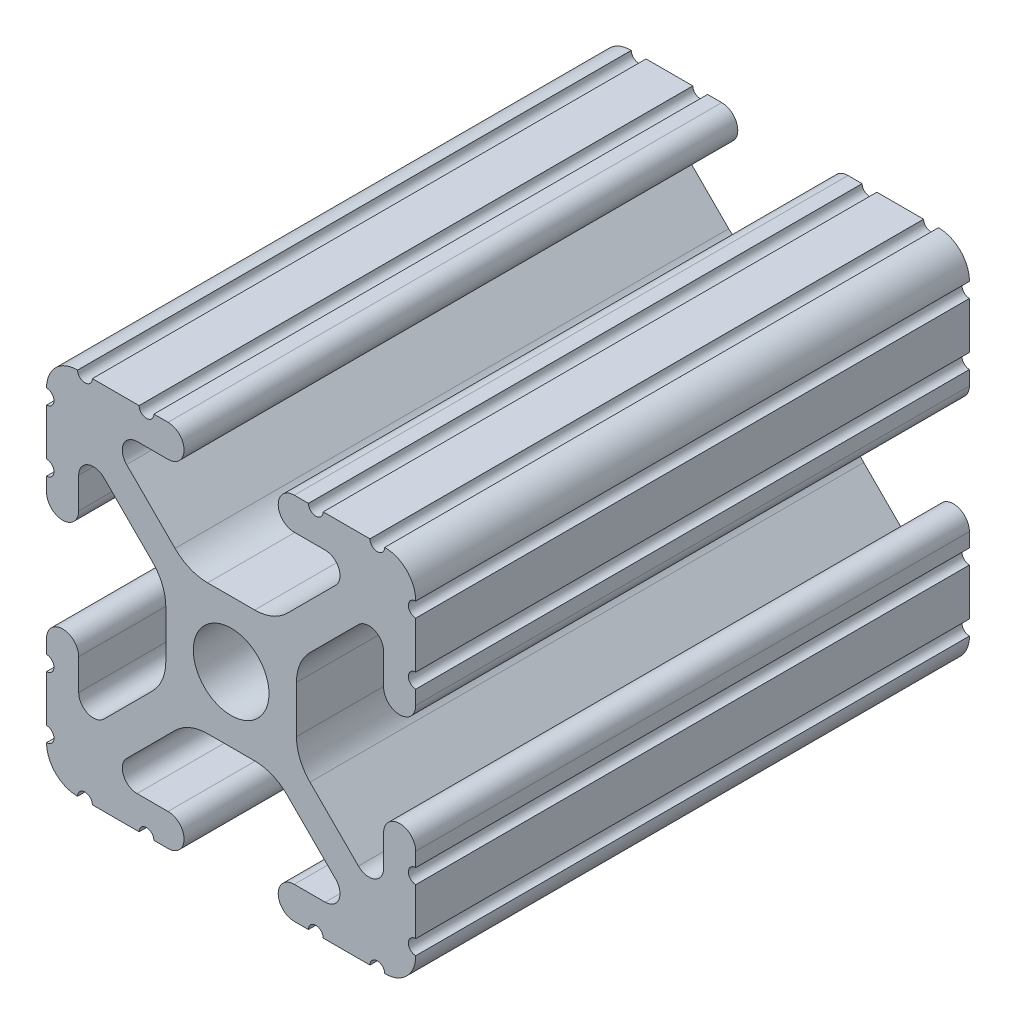
SolidWorks part; units mm, degrees
material "6061-T6 (SS)"
ref_plane "Front Plane" through (0, 0, 0) normal (0, 0, 1) x (1, 0, 0)
ref_plane "Top Plane" through (0, 0, 0) normal (0, 1, 0) x (1, 0, 0)
ref_plane "Right Plane" through (0, 0, 0) normal (1, 0, 0) x (0, 0, -1)
ref_plane "Plane1" through (0, 0, -450.85) normal (0, 0, -1) x (-1, 0, 0)
sketch "Sketch1" plane through (0, 0, -450.85) normal (0, 0, -1) x (-1, 0, 0)
  line L0 (12.7, -9.5504) -> (12.7, -6.3331)
  line L1 (12.7, -5.3171) -> (12.7, -4.3434)
  line L2 (10.4902, -4.3434) -> (10.4902, -6.4748)
  line L3 (8.7558, -7.1932) -> (5.4257, -3.8632)
  line L4 (4.4958, -1.6181) -> (4.4958, 1.6181)
  line L5 (5.4257, 3.8632) -> (8.7558, 7.1932)
  line L6 (10.4902, 6.4748) -> (10.4902, 4.3434)
  line L7 (12.7, 4.3434) -> (12.7, 5.3171)
  line L8 (12.7, 6.3331) -> (12.7, 9.5504)
  line L9 (9.5504, 12.7) -> (6.3331, 12.7)
  line L10 (5.3171, 12.7) -> (4.3434, 12.7)
  line L11 (4.3434, 10.4902) -> (6.4748, 10.4902)
  line L12 (7.1932, 8.7558) -> (3.8632, 5.4257)
  line L13 (1.6181, 4.4958) -> (-1.6181, 4.4958)
  line L14 (-3.8632, 5.4257) -> (-7.1932, 8.7558)
  line L15 (-6.4748, 10.4902) -> (-4.3434, 10.4902)
  line L16 (-4.3434, 12.7) -> (-5.3171, 12.7)
  line L17 (-6.3331, 12.7) -> (-9.5504, 12.7)
  line L18 (-12.7, 9.5504) -> (-12.7, 6.3331)
  line L19 (-12.7, 5.3171) -> (-12.7, 4.3434)
  line L20 (-10.4902, 4.3434) -> (-10.4902, 6.4748)
  line L21 (-8.7558, 7.1932) -> (-5.4257, 3.8632)
  line L22 (-4.4958, 1.6181) -> (-4.4958, -1.6181)
  line L23 (-5.4257, -3.8632) -> (-8.7558, -7.1932)
  line L24 (-10.4902, -6.4748) -> (-10.4902, -4.3434)
  line L25 (-12.7, -4.3434) -> (-12.7, -5.3171)
  line L26 (-12.7, -6.3331) -> (-12.7, -9.5504)
  line L27 (-9.5504, -12.7) -> (-6.3331, -12.7)
  line L28 (-5.3171, -12.7) -> (-4.3434, -12.7)
  line L29 (-4.3434, -10.4902) -> (-6.4748, -10.4902)
  line L30 (-7.1932, -8.7558) -> (-3.8632, -5.4257)
  line L31 (-1.6181, -4.4958) -> (1.6181, -4.4958)
  line L32 (3.8632, -5.4257) -> (7.1932, -8.7558)
  line L33 (6.4748, -10.4902) -> (4.3434, -10.4902)
  line L34 (4.3434, -12.7) -> (5.3171, -12.7)
  line L35 (6.3331, -12.7) -> (9.5504, -12.7)
  arc A0 (12.6998, -10.5664) -> (12.7, -9.5504) centre (12.7, -10.0584) cw
  arc A1 (12.7, -6.3331) -> (12.7, -5.3171) centre (12.7, -5.8251) cw
  arc A2 (12.7, -4.3434) -> (10.4902, -4.3434) centre (11.5951, -4.3434) ccw
  arc A3 (10.4902, -6.4748) -> (8.7558, -7.1932) centre (9.4742, -6.4748) cw
  arc A4 (5.4257, -3.8632) -> (4.4958, -1.6181) centre (7.6708, -1.6181) cw
  arc A5 (4.4958, 1.6181) -> (5.4257, 3.8632) centre (7.6708, 1.6181) cw
  arc A6 (8.7558, 7.1932) -> (10.4902, 6.4748) centre (9.4742, 6.4748) cw
  arc A7 (10.4902, 4.3434) -> (12.7, 4.3434) centre (11.5951, 4.3434) ccw
  arc A8 (12.7, 5.3171) -> (12.7, 6.3331) centre (12.7, 5.8251) cw
  arc A9 (12.7, 9.5504) -> (12.6998, 10.5664) centre (12.7, 10.0584) cw
  arc A10 (12.6998, 10.5664) -> (10.5664, 12.6998) centre (10.5918, 10.5918) ccw
  arc A11 (10.5664, 12.6998) -> (9.5504, 12.7) centre (10.0584, 12.7) cw
  arc A12 (6.3331, 12.7) -> (5.3171, 12.7) centre (5.8251, 12.7) cw
  arc A13 (4.3434, 12.7) -> (4.3434, 10.4902) centre (4.3434, 11.5951) ccw
  arc A14 (6.4748, 10.4902) -> (7.1932, 8.7558) centre (6.4748, 9.4742) cw
  arc A15 (3.8632, 5.4257) -> (1.6181, 4.4958) centre (1.6181, 7.6708) cw
  arc A16 (-1.6181, 4.4958) -> (-3.8632, 5.4257) centre (-1.6181, 7.6708) cw
  arc A17 (-7.1932, 8.7558) -> (-6.4748, 10.4902) centre (-6.4748, 9.4742) cw
  arc A18 (-4.3434, 10.4902) -> (-4.3434, 12.7) centre (-4.3434, 11.5951) ccw
  arc A19 (-5.3171, 12.7) -> (-6.3331, 12.7) centre (-5.8251, 12.7) cw
  arc A20 (-9.5504, 12.7) -> (-10.5664, 12.6998) centre (-10.0584, 12.7) cw
  arc A21 (-10.5664, 12.6998) -> (-12.6998, 10.5664) centre (-10.5918, 10.5918) ccw
  arc A22 (-12.6998, 10.5664) -> (-12.7, 9.5504) centre (-12.7, 10.0584) cw
  arc A23 (-12.7, 6.3331) -> (-12.7, 5.3171) centre (-12.7, 5.8251) cw
  arc A24 (-12.7, 4.3434) -> (-10.4902, 4.3434) centre (-11.5951, 4.3434) ccw
  arc A25 (-10.4902, 6.4748) -> (-8.7558, 7.1932) centre (-9.4742, 6.4748) cw
  arc A26 (-5.4257, 3.8632) -> (-4.4958, 1.6181) centre (-7.6708, 1.6181) cw
  arc A27 (-4.4958, -1.6181) -> (-5.4257, -3.8632) centre (-7.6708, -1.6181) cw
  arc A28 (-8.7558, -7.1932) -> (-10.4902, -6.4748) centre (-9.4742, -6.4748) cw
  arc A29 (-10.4902, -4.3434) -> (-12.7, -4.3434) centre (-11.5951, -4.3434) ccw
  arc A30 (-12.7, -5.3171) -> (-12.7, -6.3331) centre (-12.7, -5.8251) cw
  arc A31 (-12.7, -9.5504) -> (-12.6998, -10.5664) centre (-12.7, -10.0584) cw
  arc A32 (-12.6998, -10.5664) -> (-10.5664, -12.6998) centre (-10.5918, -10.5918) ccw
  arc A33 (-10.5664, -12.6998) -> (-9.5504, -12.7) centre (-10.0584, -12.7) cw
  arc A34 (-6.3331, -12.7) -> (-5.3171, -12.7) centre (-5.8251, -12.7) cw
  arc A35 (-4.3434, -12.7) -> (-4.3434, -10.4902) centre (-4.3434, -11.5951) ccw
  arc A36 (-6.4748, -10.4902) -> (-7.1932, -8.7558) centre (-6.4748, -9.4742) cw
  arc A37 (-3.8632, -5.4257) -> (-1.6181, -4.4958) centre (-1.6181, -7.6708) cw
  arc A38 (1.6181, -4.4958) -> (3.8632, -5.4257) centre (1.6181, -7.6708) cw
  arc A39 (7.1932, -8.7558) -> (6.4748, -10.4902) centre (6.4748, -9.4742) cw
  arc A40 (4.3434, -10.4902) -> (4.3434, -12.7) centre (4.3434, -11.5951) ccw
  arc A41 (5.3171, -12.7) -> (6.3331, -12.7) centre (5.8251, -12.7) cw
  arc A42 (9.5504, -12.7) -> (10.5664, -12.6998) centre (10.0584, -12.7) cw
  arc A43 (10.5664, -12.6998) -> (12.6998, -10.5664) centre (10.5918, -10.5918) ccw
  circle A44 centre (0, 0) radius 2.6035
extrude "Boss-Extrude1" add sketch "Sketch1" against normal mid plane 38.1
